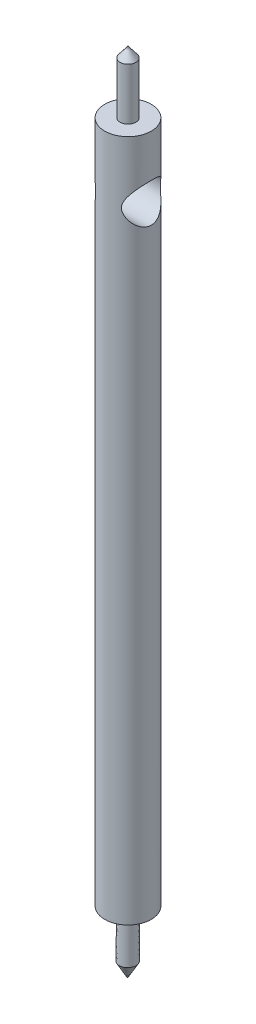
SolidWorks part; units mm, degrees
ref_plane "Front Plane" through (0, 0, 0) normal (0, 0, 1) x (1, 0, 0)
ref_plane "Top Plane" through (0, 0, 0) normal (0, 1, 0) x (1, 0, 0)
ref_plane "Right Plane" through (0, 0, 0) normal (1, 0, 0) x (0, 0, -1)
sketch "Sketch1" plane through (0, 0, 0) normal (0, 1, 0) x (1, 0, 0)
  line L0 (-2.6194, 0) -> (2.6194, 0) construction
  circle A0 centre (0, 0) radius 2.3813
extrude "Boss-Extrude1" add sketch "Sketch1" along normal blind 69.85
sketch "Sketch2" plane through (0, 0, 0) normal (0, 0, 1) x (1, 0, 0)
  line L0 (0, 76.2) -> (0, 69.85)
  line L2 (0.8128, 75.1578) -> (0.8128, 69.85)
  line L3 (2.3813, 69.85) -> (-2.3813, 69.85) construction
  line L4 (0, 79.244) -> (0, -16.7044) construction
  line L6 (0, 76.2) -> (0.8128, 75.1578)
  line L7 (0, 69.85) -> (0.8128, 69.85)
revolve "Revolve4" add sketch "Sketch2" angle 360 about L4
sketch "Sketch4" plane through (0, 0, 0) normal (1, 0, 0) x (0, 0, -1)
  line L0 (0, 0) -> (-0.0541, -6.35)
  line L1 (-0.0541, -6.35) -> (0.8128, -4.8486)
  line L2 (0.8128, -4.8486) -> (0.8128, 0)
  line L3 (-2.3813, 0) -> (2.3813, 0) construction
  line L4 (0, 0) -> (0.8128, 0)
revolve "Revolve5" add sketch "Sketch4" angle 360 about L0
sketch "Sketch7" plane through (0, 0, 0) normal (1, 0, 0) x (0, 0, -1)
  circle A0 centre (0, 63.5) radius 1.9844
extrude "Cut-Extrude1" cut sketch "Sketch7" against normal through all both and the other way through all
